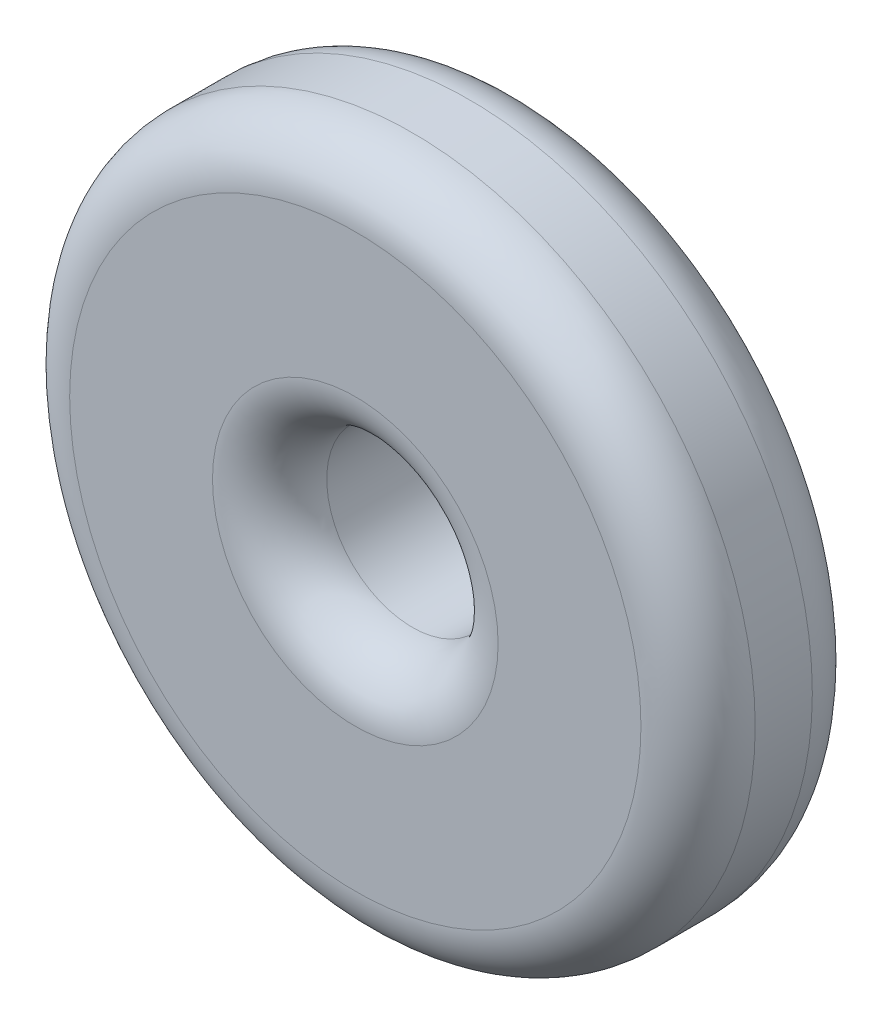
SolidWorks part; units mm, degrees
ref_plane "前视基准面" through (0, 0, 0) normal (0, 0, 1) x (1, 0, 0)
ref_plane "上视基准面" through (0, 0, 0) normal (0, 1, 0) x (1, 0, 0)
ref_plane "右视基准面" through (0, 0, 0) normal (1, 0, 0) x (0, 0, -1)
sketch "草图1" plane through (0, 0, 0) normal (0, 0, 1) x (1, 0, 0)
  circle A1 centre (0, 0) radius 1.5
  circle A2 centre (0, 0) radius 6
extrude "凸台-拉伸1" add sketch "草图1" along normal blind 3 contours A2 | A1
fillet "圆角2" radius 1 1 edges at (6, 0, 0)
fillet "圆角3" radius 1 2 edges at (1.5, 0, 3) (6, 0, 3)
